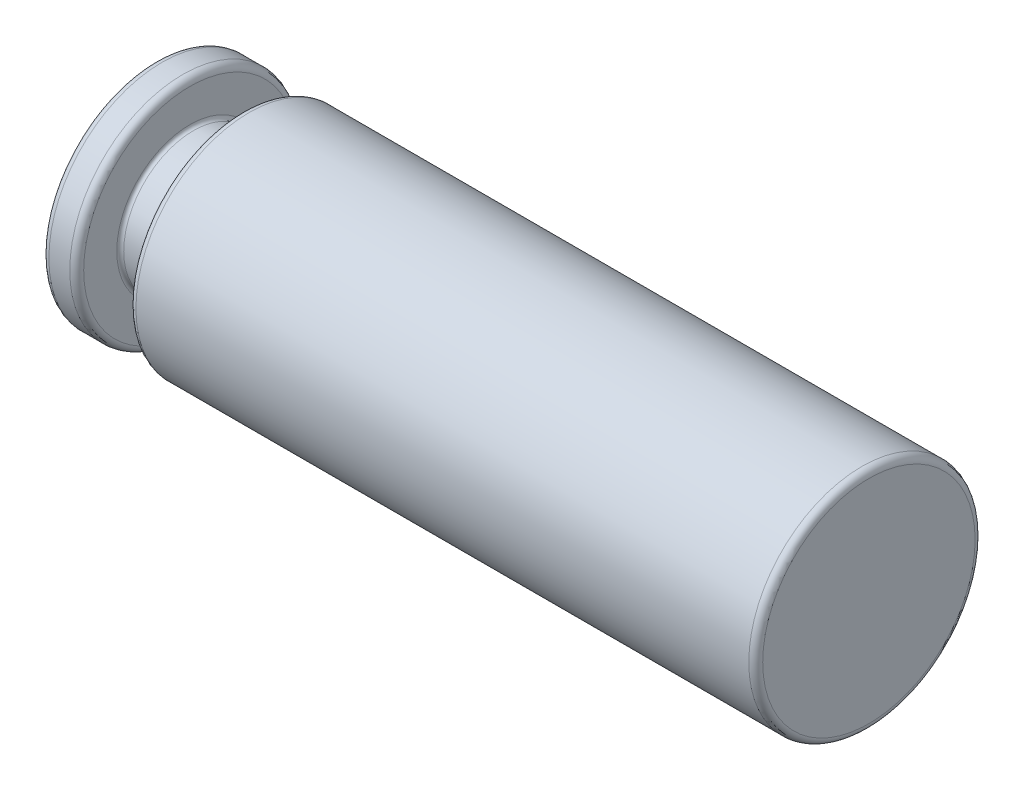
SolidWorks part; units mm, degrees
ref_plane "Plane1" through (0, 0, 0) normal (0, 0, 1) x (1, 0, 0)
ref_plane "Plane2" through (0, 0, 0) normal (0, 1, 0) x (1, 0, 0)
ref_plane "Plane3" through (0, 0, 0) normal (1, 0, 0) x (0, 0, -1)
sketch "Sketch1" plane through (0, 0, 0) normal (0, 0, 1) x (1, 0, 0)
  line L0 (0, 0) -> (82, 0) construction
  line L1 (0, 0) -> (0, 12.2)
  line L2 (0.8, 13) -> (3.2, 13)
  line L3 (4, 12.2) -> (4, 8.4)
  line L4 (4.4, 8) -> (9.6, 8)
  line L5 (10, 8.4) -> (10, 12.2)
  line L6 (10.8, 13) -> (81.2, 13)
  line L7 (82, 12.2) -> (82, 0)
  line L8 (0, 0) -> (82, 0)
  arc A0 (82, 12.2) -> (81.2, 13) centre (81.2, 12.2) ccw
  arc A1 (10.8, 13) -> (10, 12.2) centre (10.8, 12.2) ccw
  arc A2 (0.8, 13) -> (0, 12.2) centre (0.8, 12.2) ccw
  arc A3 (4, 12.2) -> (3.2, 13) centre (3.2, 12.2) ccw
  arc A4 (10, 8.4) -> (9.6, 8) centre (9.6, 8.4) cw
  arc A5 (4.4, 8) -> (4, 8.4) centre (4.4, 8.4) cw
  dimension "D7" = 0.8
  dimension "D8" = 0.4
  dimension "D1" = 26
  dimension "D2" = 16
  dimension "D4" = 72
  dimension "D5" = 6
  dimension "D6" = 82
  dimension "D9" = 4
revolve "Base-Revolve" add sketch "Sketch1" angle 360 about L0
